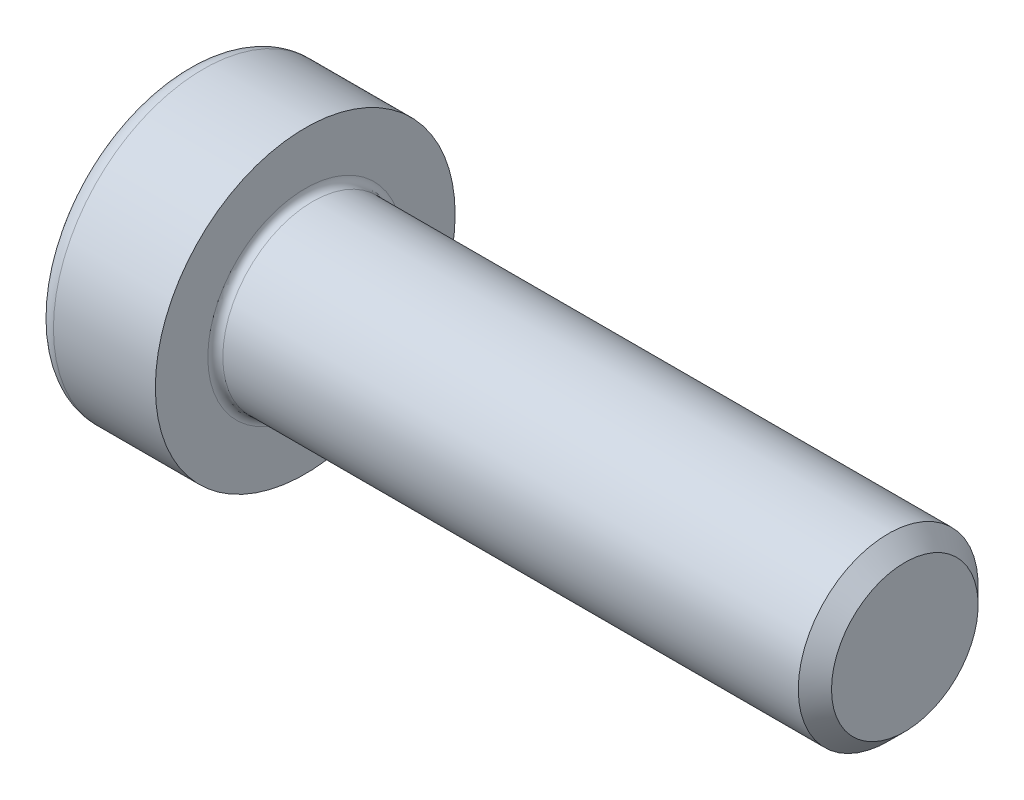
SolidWorks part; units mm, degrees
revolve "Base-Revolve" add sketch "BodySke"
sketch "BodySke" plane through (0, 0, 0) normal (0, 0, 1) x (1, 0, 0)
  line L0 (0, 0) -> (0, 5)
  line L1 (0, 5) -> (4, 5)
  line L2 (4, 5) -> (4, 3)
  line L3 (4, 3) -> (23.4455, 3)
  line L4 (24, 2.4455) -> (24, 0)
  line L5 (24, 0) -> (0, 0)
  line L6 (-31.75, 0) -> (127, 0) construction
  line L8 (24, 2.4455) -> (23.4455, 3)
  line L10 (24, -2.4455) -> (23.4455, -3) construction
  line L11 (5, 4.525) -> (5, -1.825) construction
  line L12 (4, 4.525) -> (4, -1.825) construction
  line L13 (-36, 4.525) -> (-36, -1.825) construction
  dimension "Head_ht" = 4
  dimension "Length" = 20
  dimension "Body_ch_ang" = 45
  dimension "Diameter" = 6
  dimension "Minor_dia" = 4.891
  dimension "Advance" = 1
  dimension "Thread_nom" = 20
  dimension "Thread_length" = 60
  dimension "Head_dia" = 10
cosmetic thread "ThreadCosmetic" [suppressed]
fillet "Fillet1" radius 0.25 1 edges at (4, 0, 3)
fillet "Fillet2" radius 0.6 1 edges at (0, 0, 5)
ref_plane "Plane1" through (0, 0, 0) normal (0, 0, 1) x (1, 0, 0)
ref_plane "Plane2" through (0, 0, 0) normal (0, 1, 0) x (1, 0, 0)
ref_plane "Plane3" through (0, 0, 0) normal (1, 0, 0) x (0, 0, -1)
sketch "HexSke" plane through (0, 0, 0) normal (-1, 0, 0) x (0, 0.5, 0.866)
  line L0 (1.4434, 2.5) -> (-1.4434, 2.5)
  line L1 (-1.4434, 2.5) -> (-2.8868, 0)
  line L2 (1.4434, 2.5) -> (2.8868, 0)
  line L3 (1.4434, -2.5) -> (2.8868, 0)
  line L4 (1.4434, -2.5) -> (-1.4434, -2.5)
  line L5 (-1.4434, -2.5) -> (-2.8868, 0)
  dimension "D1" = 2.5
  dimension "D2" = 2.5
  dimension "Hex_size" = 5
extrude "Hex" cut sketch "HexSke" against normal blind 2.5
sketch "PilotSke" plane through (0, 0, 0) normal (0, 0, 1) x (1, 0, 0)
  line L0 (0, 2.5) -> (2.5, 2.5)
  line L1 (2.5, 2.5) -> (3.0774, 1.5)
  line L2 (-31.75, 0) -> (127, 0) construction
  line L3 (5.866, 0) -> (0, 0)
  line L4 (0, 0) -> (0, 2.5)
  line L5 (3.0774, 1.5) -> (5, 1.5)
  line L6 (0, 0) -> (47.625, 0) construction
  line L7 (5, 1.5) -> (5.866, 0)
  dimension "D1" = 2.5
  dimension "D2" = 60
  dimension "Depth" = 2.5
  dimension "Pilot_dia" = 3
  dimension "Pilot_Depth" = 5
revolve "Hex-PreBroach" cut sketch "PilotSke" angle 360 about L6
sketch "ThdSchSke" plane through (0, 0, 0) normal (0, 0, 1) x (1, 0, 0)
  line L0 (7, -2.4455) -> (6.6117, -3)
  line L1 (7, -2.4455) -> (7.3883, -3)
  line L2 (7.3883, -3) -> (7.3883, -3.75)
  line L3 (-3.175, 0) -> (5.1513, 0) construction
  line L4 (0, 4.4) -> (0, -4.4) construction
  line L5 (7.3883, -3.75) -> (6.6117, -3.75)
  line L6 (6.6117, -3.75) -> (6.6117, -3)
  dimension "Thread_minor" = 4.891
  dimension "Diameter" = 6
  dimension "Start" = 7
revolve "ThreadSchematic" [suppressed] cut sketch "ThdSchSke" angle 360 about L3
pattern_linear "ThdSchPat" [suppressed]
equation "\"D2@HexSke\" = \"Hex_size@HexSke\" / 2"
equation "\"D1@HexSke\" = \"Hex_size@HexSke\" / 2"
equation "\"D1@PilotSke\" = \"Hex_size@HexSke\" / 2"
equation "\"Thread_minor@ThreadCosmetic\"  =  \"Minor_dia@BodySke\""
equation "\"Depth@PilotSke\" =  \"Key_eng@Hex\""
equation "\"Thread_length@ThreadCosmetic\" = ((sgn( (\"Length@BodySke\" - \"Advance@BodySke\" * 3.0) - \"Thread_nom@BodySke\" )-1)*( (\"Length@BodySke\" - \"Advance@BodySke\" * 3.0) - \"Thread_nom@BodySke\" ))/-2+ \"Thread_nom@BodySke\""
equation "\"Thread_minor@ThdSchSke\" = \"Minor_dia@BodySke\""
equation "\"Diameter@ThdSchSke\" = \"Diameter@BodySke\""
equation "\"Overcut@ThdSchSke\" = \"Diameter@BodySke\" * 1.25"
equation "\"Start@ThdSchSke\" = \"Head_ht@BodySke\" + \"Length@BodySke\" - \"Thread_length@ThreadCosmetic\"  '---Non-countersunk---"
equation "\"Num_threads@ThdSchPat\" = int( \"Thread_length@ThreadCosmetic\" / \"Advance@BodySke\" + 0.999 )  + 1"
equation "\"Advance@ThdSchPat\" = \"Thread_length@ThreadCosmetic\" /  (\"Num_threads@ThdSchPat\" - 1) 'relax it"
equation "\"Num_threads@ThdSchPat\" = \"Num_threads@ThdSchPat\" - sgn( \"Num_threads@ThdSchPat\" - 1) '---chamfered tips only---"
